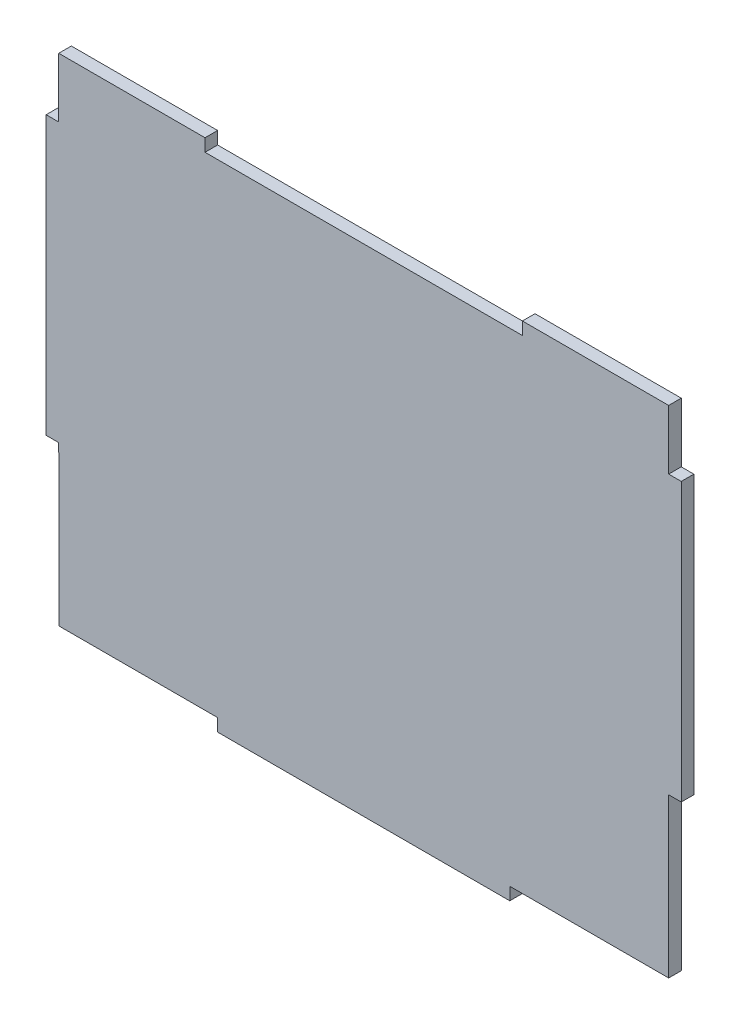
SolidWorks part; units mm, degrees
ref_plane "Front Plane" through (0, 0, 0) normal (0, 0, 1) x (1, 0, 0)
ref_plane "Top Plane" through (0, 0, 0) normal (0, 1, 0) x (1, 0, 0)
ref_plane "Right Plane" through (0, 0, 0) normal (1, 0, 0) x (0, 0, -1)
sketch "Sketch1" plane through (0, 0, 0) normal (0, 0, 1) x (1, 0, 0)
  line L0 (-127.3825, 0) -> (127.9461, 0) construction
  line L1 (0, 75.2459) -> (0, -162.0775) construction
  line L2 (-76.875, 0) -> (76.875, 0)
  line L3 (76.875, 0) -> (76.875, -15)
  line L4 (76.875, -15) -> (80.05, -15)
  line L5 (80.05, -15) -> (80.05, -85)
  line L6 (80.05, -85) -> (76.875, -85)
  line L7 (76.875, -85) -> (76.875, -125)
  line L9 (36.825, -128.175) -> (36.825, -125)
  line L11 (-36.825, -128.175) -> (-36.825, -125)
  line L13 (-76.875, -85) -> (-76.825, -125)
  line L14 (-80.05, -85) -> (-76.875, -85)
  line L15 (-80.05, -15) -> (-80.05, -85)
  line L16 (-76.875, -15) -> (-80.05, -15)
  line L17 (-76.875, 0) -> (-76.875, -15)
  line L18 (-36.825, -128.175) -> (36.825, -128.175)
  line L19 (-76.825, -125) -> (-36.825, -125)
  line L20 (36.825, -125) -> (76.875, -125)
  point P16 (0, -125)
  point P17 (0, 0)
  dimension "D1" = 76.875
  dimension "D2" = 15
  dimension "D3" = 3.175
  dimension "D4" = 70
  dimension "D5" = 3.175
  dimension "D6" = 40
  dimension "D7" = 40
  dimension "D8" = 3.175
  dimension "D9" = 36.825
extrude "Boss-Extrude2" add sketch "Sketch1" along normal blind 3.175
ref_plane "Plane1" through (0, 0, 3.175) normal (0, 0, 1) x (1, 0, 0)
sketch "Sketch2" plane through (0, 0, 3.175) normal (0, 0, 1) x (1, 0, 0)
  line L0 (0, 23.3225) -> (0, -169.3894) construction
  line L3 (76.875, 0) -> (-76.875, 0) construction
  line L4 (40, 0) -> (40, -3.175)
  line L5 (40, -3.175) -> (-40, -3.175)
  line L6 (-40, -3.175) -> (-40, 0)
  line L7 (-40, 0) -> (40, 0)
  dimension "D2" = 3.175
  dimension "D3" = 80
extrude "Cut-Extrude1" cut sketch "Sketch2" against normal through all
